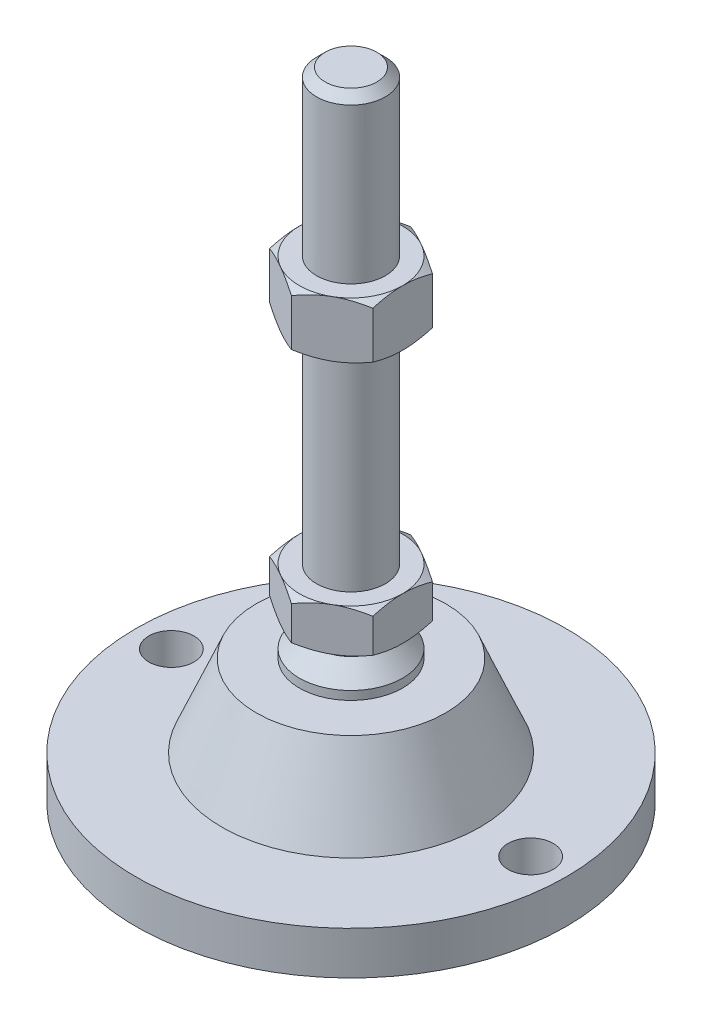
SolidWorks part; units mm, degrees
ref_plane "Спереди" through (0, 0, 0) normal (0, 0, 1) x (1, 0, 0)
ref_plane "Сверху" through (0, 0, 0) normal (0, 1, 0) x (1, 0, 0)
ref_plane "Справа" through (0, 0, 0) normal (1, 0, 0) x (0, 0, -1)
sketch "Эскиз1" plane through (0, 0, 0) normal (0, 0, 1) x (1, 0, 0)
  line L0 (0, 0) -> (-50, 0)
  line L3 (-50, 0) -> (-50, 10)
  line L12 (-8, 48) -> (-8, 146)
  line L13 (-8, 146) -> (-6, 148)
  line L14 (-6, 148) -> (0, 148)
  line L15 (0, 148) -> (0, 0) construction
  line L16 (-50, 10) -> (-30, 10)
  line L17 (0, 0) -> (0, 148)
  line L18 (0, 0) -> (0, -7.9595) construction
  line L19 (-8, 48) -> (-8, 38)
  line L21 (-12, 29) -> (-22, 29)
  line L22 (-30, 10) -> (-22, 29)
  line L23 (-12, 29) -> (-12, 31)
  line L24 (-12, 31) -> (-8, 35)
  line L25 (-8, 35) -> (-8, 38)
  line L26 (-8, 48) -> (0, 48) construction
  point P8 (-8, 97)
revolve "Повернуть1" add sketch "Эскиз1" angle 360 about L17
ref_plane "Плоскость2" through (0, 38, 0) normal (0, 1, 0) x (1, 0, 0)
sketch "Эскиз2" plane through (0, 38, 0) normal (0, 1, 0) x (1, 0, 0)
  line L1 (0, 13.8564) -> (-12, 6.9282)
  line L2 (-12, 6.9282) -> (-12, -6.9282)
  line L3 (-12, -6.9282) -> (0, -13.8564)
  line L4 (0, -13.8564) -> (12, -6.9282)
  line L5 (12, -6.9282) -> (12, 6.9282)
  line L6 (12, 6.9282) -> (0, 13.8564)
  circle A0 centre (0, 0) radius 12 construction
  dimension "D1" = 24
extrude "Бобышка-Вытянуть1" add sketch "Эскиз2" along normal up to vertex (10 mm away) up to point (-8, 48, 0)
ref_plane "Плоскость1" through (0, 97, 0) normal (0, 1, 0) x (1, 0, 0)
sketch "Эскиз3" plane through (0, 97, 0) normal (0, 1, 0) x (1, 0, 0)
  line L6 (12, 6.9282) -> (0, 13.8564)
  line L7 (0, 13.8564) -> (-12, 6.9282)
  line L8 (-12, 6.9282) -> (-12, -6.9282)
  line L9 (-12, -6.9282) -> (0, -13.8564)
  line L10 (0, -13.8564) -> (12, -6.9282)
  line L11 (12, -6.9282) -> (12, 6.9282)
  line L12 (12, 6.9282) -> (0, 13.8564)
  line L13 (0, 13.8564) -> (-12, 6.9282)
  line L14 (-12, 6.9282) -> (-12, -6.9282)
  line L15 (-12, -6.9282) -> (0, -13.8564)
  line L16 (0, -13.8564) -> (12, -6.9282)
  line L17 (12, -6.9282) -> (12, 6.9282)
  dimension "D1" = 0
extrude "Бобышка-Вытянуть2" add sketch "Эскиз3" along normal blind 13
sketch "Эскиз4" plane through (0, 0, 0) normal (0, 0, 1) x (1, 0, 0)
  line L0 (-12, 110) -> (-23.2583, 103.5)
  line L1 (-23.2583, 103.5) -> (-23.2583, 110)
  line L2 (-23.2583, 110) -> (-12, 110)
  line L3 (-23.2583, 103.5) -> (-12, 97)
  line L4 (50, 97) -> (-50, 97) construction
  line L5 (-12, 97) -> (-23.2583, 97)
  line L6 (-23.2583, 97) -> (-23.2583, 103.5)
  line L7 (-12, 110) -> (-12, 97) construction
  line L8 (-12, 48) -> (-20.6603, 48)
  line L9 (-20.6603, 48) -> (-20.6603, 43)
  line L10 (-20.6603, 43) -> (-12, 48)
  line L11 (-12, 38) -> (-20.6603, 43)
  line L12 (-20.6603, 43) -> (-20.6603, 38)
  line L13 (-20.6603, 38) -> (-12, 38)
  line L14 (0, 148) -> (0, 96.3793) construction
  line L15 (50, 38) -> (-50, 38) construction
  dimension "D1" = 30
  dimension "D2" = 30
revolve "Вырез-Повернуть2" cut sketch "Эскиз4" angle 360 about L14
sketch "Эскиз5" plane through (0, 10, 0) normal (0, 1, 0) x (1, 0, 0)
  line L0 (41.75, 0) -> (-41.75, 0) construction
  circle A0 centre (-41.75, 0) radius 5.25
  circle A1 centre (41.75, 0) radius 5.25
  circle A2 centre (0, 0) radius 50 construction
  dimension "D1" = 10.5
  dimension "D2" = 3
extrude "Вырез-Вытянуть1" cut sketch "Эскиз5" against normal through all
equation "\"D13@Эскиз1\"=\"D12@Эскиз1\"/2"
